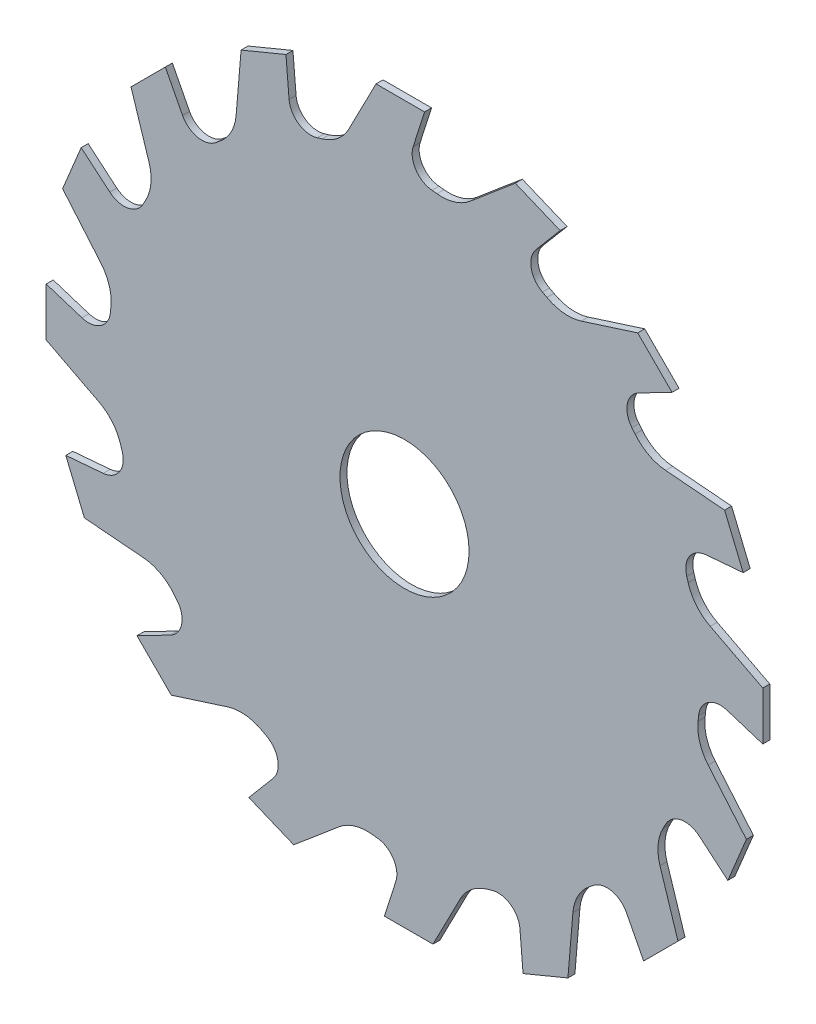
SolidWorks part; units mm, degrees
ref_plane "Front Plane" through (0, 0, 0) normal (0, 0, 1) x (1, 0, 0)
ref_plane "Top Plane" through (0, 0, 0) normal (0, 1, 0) x (1, 0, 0)
ref_plane "Right Plane" through (0, 0, 0) normal (1, 0, 0) x (0, 0, -1)
sketch "Sketch1" plane through (0, 0, 0) normal (0, 0, 1) x (1, 0, 0)
  line L0 (-6.4571, 35.4809) -> (-3.3059, 41.5877)
  line L1 (1.0071, 37.443) -> (2.3308, 41.5877)
  line L2 (2.3308, 41.5877) -> (-3.3059, 41.5877)
  line L3 (7.6124, 35.2511) -> (12.8607, 39.6872)
  line L4 (18.0683, 37.5301) -> (12.8607, 39.6872)
  line L5 (15.2592, 34.2075) -> (18.0683, 37.5301)
  line L6 (20.5229, 29.6546) -> (27.0694, 31.7446)
  line L7 (31.0551, 27.7588) -> (27.0694, 31.7446)
  line L8 (27.1883, 25.7641) -> (31.0551, 27.7588)
  line L9 (30.309, 19.5435) -> (37.1569, 18.9692)
  line L10 (39.314, 13.7615) -> (37.1569, 18.9692)
  line L11 (34.9782, 13.3984) -> (39.314, 13.7615)
  line L12 (35.4809, 6.4571) -> (41.5877, 3.3059)
  line L13 (41.5877, -2.3308) -> (41.5877, 3.3059)
  line L14 (37.443, -1.0071) -> (41.5877, -2.3308)
  line L15 (35.2511, -7.6124) -> (39.6872, -12.8607)
  line L16 (37.5301, -18.0683) -> (39.6872, -12.8607)
  line L17 (34.2075, -15.2592) -> (37.5301, -18.0683)
  line L18 (29.6546, -20.5229) -> (31.7446, -27.0694)
  line L19 (27.7588, -31.0551) -> (31.7446, -27.0694)
  line L20 (25.7641, -27.1883) -> (27.7588, -31.0551)
  line L21 (19.5435, -30.309) -> (18.9692, -37.1569)
  line L22 (13.7615, -39.314) -> (18.9692, -37.1569)
  line L23 (13.3984, -34.9782) -> (13.7615, -39.314)
  line L24 (6.4571, -35.4809) -> (3.3059, -41.5877)
  line L25 (-2.3308, -41.5877) -> (3.3059, -41.5877)
  line L26 (-1.0071, -37.443) -> (-2.3308, -41.5877)
  line L27 (-7.6124, -35.2511) -> (-12.8607, -39.6872)
  line L28 (-18.0683, -37.5301) -> (-12.8607, -39.6872)
  line L29 (-15.2592, -34.2075) -> (-18.0683, -37.5301)
  line L30 (-20.5229, -29.6546) -> (-27.0694, -31.7446)
  line L31 (-31.0551, -27.7588) -> (-27.0694, -31.7446)
  line L32 (-27.1883, -25.7641) -> (-31.0551, -27.7588)
  line L33 (-30.309, -19.5435) -> (-37.1569, -18.9692)
  line L34 (-39.314, -13.7615) -> (-37.1569, -18.9692)
  line L35 (-34.9782, -13.3984) -> (-39.314, -13.7615)
  line L36 (-35.4809, -6.4571) -> (-41.5877, -3.3059)
  line L37 (-41.5877, 2.3308) -> (-41.5877, -3.3059)
  line L38 (-37.443, 1.0071) -> (-41.5877, 2.3308)
  line L39 (-35.2511, 7.6124) -> (-39.6872, 12.8607)
  line L40 (-37.5301, 18.0683) -> (-39.6872, 12.8607)
  line L41 (-34.2075, 15.2592) -> (-37.5301, 18.0683)
  line L42 (-29.6546, 20.5229) -> (-31.7446, 27.0694)
  line L43 (-27.7588, 31.0551) -> (-31.7446, 27.0694)
  line L44 (-25.7641, 27.1883) -> (-27.7588, 31.0551)
  line L45 (-19.5435, 30.309) -> (-18.9692, 37.1569)
  line L46 (-13.7615, 39.314) -> (-18.9692, 37.1569)
  line L47 (-13.3984, 34.9782) -> (-13.7615, 39.314)
  arc A0 (-9.5558, 32.9316) -> (-10.1178, 32.7633) centre (0, 0) ccw
  arc A1 (-6.4571, 35.4809) -> (-9.5558, 32.9316) centre (-10.9715, 37.8104) cw
  arc A2 (1.0071, 37.443) -> (3.1903, 34.1413) centre (3.4266, 36.6702) ccw
  arc A3 (7.6124, 35.2511) -> (3.774, 34.0817) centre (4.3331, 39.1308) cw
  arc A4 (15.2592, 34.2075) -> (16.0128, 30.3215) centre (17.1989, 32.5676) ccw
  arc A5 (20.5229, 29.6546) -> (16.5292, 30.0431) centre (18.9779, 34.494) cw
  arc A6 (27.1883, 25.7641) -> (26.3974, 21.8856) centre (28.3528, 23.5068) ccw
  arc A7 (30.309, 19.5435) -> (26.768, 21.4308) centre (30.7336, 24.6057) cw
  arc A8 (34.9782, 13.3984) -> (32.7633, 10.1178) centre (35.1902, 10.8673) ccw
  arc A9 (35.4809, 6.4571) -> (32.9316, 9.5558) centre (37.8104, 10.9715) cw
  arc A10 (37.443, -1.0071) -> (34.1413, -3.1903) centre (36.6702, -3.4266) ccw
  arc A11 (35.2511, -7.6124) -> (34.0817, -3.774) centre (39.1308, -4.3331) cw
  arc A12 (34.2075, -15.2592) -> (30.3215, -16.0128) centre (32.5676, -17.1989) ccw
  arc A13 (29.6546, -20.5229) -> (30.0431, -16.5292) centre (34.494, -18.9779) cw
  arc A14 (25.7641, -27.1883) -> (21.8856, -26.3974) centre (23.5068, -28.3528) ccw
  arc A15 (19.5435, -30.309) -> (21.4308, -26.768) centre (24.6057, -30.7336) cw
  arc A16 (13.3984, -34.9782) -> (10.1178, -32.7633) centre (10.8673, -35.1902) ccw
  arc A17 (6.4571, -35.4809) -> (9.5558, -32.9316) centre (10.9715, -37.8104) cw
  arc A18 (-1.0071, -37.443) -> (-3.1903, -34.1413) centre (-3.4266, -36.6702) ccw
  arc A19 (-7.6124, -35.2511) -> (-3.774, -34.0817) centre (-4.3331, -39.1308) cw
  arc A20 (-15.2592, -34.2075) -> (-16.0128, -30.3215) centre (-17.1989, -32.5676) ccw
  arc A21 (-20.5229, -29.6546) -> (-16.5292, -30.0431) centre (-18.9779, -34.494) cw
  arc A22 (-27.1883, -25.7641) -> (-26.3974, -21.8856) centre (-28.3528, -23.5068) ccw
  arc A23 (-30.309, -19.5435) -> (-26.768, -21.4308) centre (-30.7336, -24.6057) cw
  arc A24 (-34.9782, -13.3984) -> (-32.7633, -10.1178) centre (-35.1902, -10.8673) ccw
  arc A25 (-35.4809, -6.4571) -> (-32.9316, -9.5558) centre (-37.8104, -10.9715) cw
  arc A26 (-37.443, 1.0071) -> (-34.1413, 3.1903) centre (-36.6702, 3.4266) ccw
  arc A27 (-35.2511, 7.6124) -> (-34.0817, 3.774) centre (-39.1308, 4.3331) cw
  arc A28 (-34.2075, 15.2592) -> (-30.3215, 16.0128) centre (-32.5676, 17.1989) ccw
  arc A29 (-29.6546, 20.5229) -> (-30.0431, 16.5292) centre (-34.494, 18.9779) cw
  arc A30 (-25.7641, 27.1883) -> (-21.8856, 26.3974) centre (-23.5068, 28.3528) ccw
  arc A31 (-19.5435, 30.309) -> (-21.4308, 26.768) centre (-24.6057, 30.7336) cw
  arc A32 (-13.3984, 34.9782) -> (-10.1178, 32.7633) centre (-10.8673, 35.1902) ccw
  arc A33 (-21.4308, 26.768) -> (-21.8856, 26.3974) centre (0, 0) ccw
  arc A34 (-30.0431, 16.5292) -> (-30.3215, 16.0128) centre (0, 0) ccw
  arc A35 (-34.0817, 3.774) -> (-34.1413, 3.1903) centre (0, 0) ccw
  arc A36 (-32.9316, -9.5558) -> (-32.7633, -10.1178) centre (0, 0) ccw
  arc A37 (-26.768, -21.4308) -> (-26.3974, -21.8856) centre (0, 0) ccw
  arc A38 (-16.5292, -30.0431) -> (-16.0128, -30.3215) centre (0, 0) ccw
  arc A39 (-3.774, -34.0817) -> (-3.1903, -34.1413) centre (0, 0) ccw
  arc A40 (9.5558, -32.9316) -> (10.1178, -32.7633) centre (0, 0) ccw
  arc A41 (21.4308, -26.768) -> (21.8856, -26.3974) centre (0, 0) ccw
  arc A42 (30.0431, -16.5292) -> (30.3215, -16.0128) centre (0, 0) ccw
  arc A43 (34.0817, -3.774) -> (34.1413, -3.1903) centre (0, 0) ccw
  arc A44 (32.9316, 9.5558) -> (32.7633, 10.1178) centre (0, 0) ccw
  arc A45 (26.768, 21.4308) -> (26.3974, 21.8856) centre (0, 0) ccw
  arc A46 (16.5292, 30.0431) -> (16.0128, 30.3215) centre (0, 0) ccw
  arc A47 (3.774, 34.0817) -> (3.1903, 34.1413) centre (0, 0) ccw
  circle A48 centre (0, 0) radius 7.493
  point P8 (-7.5, 33.4597)
  point P11 (0, 34.29)
  point P135 (0, 0)
  dimension "D1" = 68.58
  dimension "D3" = 5.08
  dimension "D4" = 2.54
  dimension "D6" = 14.986
  dimension "D2" = 8.128
  dimension "D5" = 16
extrude "Boss-Extrude1" add sketch "Sketch1" along normal blind 0.8128
